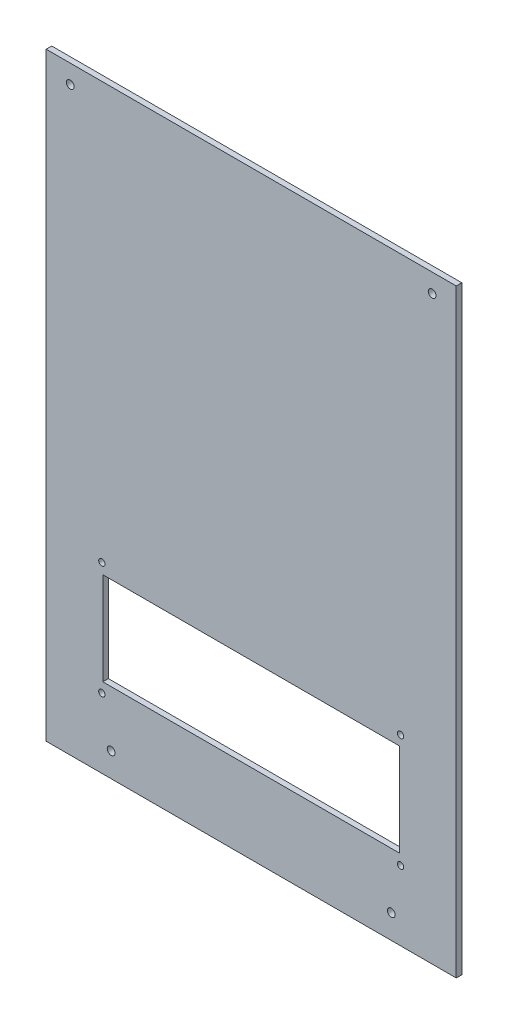
SolidWorks part; units mm, degrees
material "ABS PC"
ref_plane "Front Plane" through (0, 0, 0) normal (0, 0, 1) x (1, 0, 0)
ref_plane "Top Plane" through (0, 0, 0) normal (0, 1, 0) x (1, 0, 0)
ref_plane "Right Plane" through (0, 0, 0) normal (1, 0, 0) x (0, 0, -1)
sketch "Sketch1" plane through (0, 0, -125.5) normal (0, 0, -1) x (-1, 0, 0)
  line L1 (-110.5, 310) -> (110.5, 310)
  line L2 (-110.5, 310) -> (-110.5, -13)
  line L3 (-110.5, -13) -> (110.5, -13)
  line L4 (110.5, 310) -> (110.5, -13)
extrude "Boss-Extrude1" add sketch "Sketch1" against normal up to vertex (3 mm away)
sketch "Sketch2" plane through (0, 0, -122.5) normal (0, 0, 1) x (1, 0, 0)
  line L0 (110.5, -13) -> (-110.5, -13) construction
  line L1 (-80, 80) -> (80, 80)
  line L2 (-80, 80) -> (-80, 30)
  line L3 (-80, 30) -> (80, 30)
  line L4 (80, 80) -> (80, 30)
  line L6 (110.5, 310) -> (110.5, -13) construction
  line L7 (-110.5, -13) -> (-110.5, 310) construction
  dimension "D1" = 43
  dimension "D3" = 30.5
  dimension "D4" = 50
  dimension "D2" = 30.5
extrude "Cut-Extrude1" cut sketch "Sketch2" against normal through all
sketch "Sketch5" plane through (0, 0, -125.5) normal (0, 0, -1) x (-1, 0, 0)
  line L0 (-110.5, -13) -> (110.5, -13) construction
  line L1 (-80.5, 85.5) -> (80.5, 85.5) construction
  line L2 (-80.5, 85.5) -> (-80.5, 24.5) construction
  line L3 (-80.5, 24.5) -> (80.5, 24.5) construction
  line L4 (80.5, 85.5) -> (80.5, 24.5) construction
  line L5 (0, 0) -> (0, 24.5) construction
  circle A0 centre (80.5, 85.5) radius 1.7
  circle A1 centre (80.5, 24.5) radius 1.7
  circle A2 centre (-80.5, 24.5) radius 1.7
  circle A3 centre (-80.5, 85.5) radius 1.7
  dimension "D1" = 3.4
  dimension "D2" = 161
  dimension "D3" = 61
  dimension "D4" = 37.5
extrude "Cut-Extrude2" cut sketch "Sketch5" against normal up to next
hole_wizard "Ø4.0mm Dowel Hole1" positions "Sketch6" profile "Sketch8" hole size "Ø4.0" standard "ISO" end condition up to next
sketch "Sketch6" plane through (0, 0, -122.5) normal (0, 0, 1) x (1, 0, 0)
  line L0 (-110.5, -13) -> (-110.5, 310) construction
  line L1 (-110.5, 310) -> (110.5, 310) construction
  line L2 (110.5, 310) -> (110.5, -13) construction
  line L3 (110.5, -13) -> (-110.5, -13) construction
  point P603 (-97.5, 300)
  point P605 (97.5, 300)
  point P607 (75.5, 0)
  point P609 (-75.5, 0)
  dimension "D1" = 13
  dimension "D2" = 10
  dimension "D3" = 13
  dimension "D4" = 10
  dimension "D5" = 35
  dimension "D6" = 13
  dimension "D7" = 35
  dimension "D8" = 13
sketch "Sketch8" plane through (-97.5, 300, -122.5) normal (1, 0, 0) x (0, -1, 0)
  line L0 (0, 0) -> (0, 3)
  line L1 (0, 3) -> (2.1, 3)
  line L2 (2.1, 3) -> (2.1, 0)
  line L5 (2.1, 0) -> (0, 0)
  line L11 (0, -6.35) -> (0, 107.95) construction
  dimension "Thru Hole Dia." = 4.2
  dimension "Thru Hole Depth" = 3
equation "\"D2@Sketch2\"=\"D3@Sketch2\""
